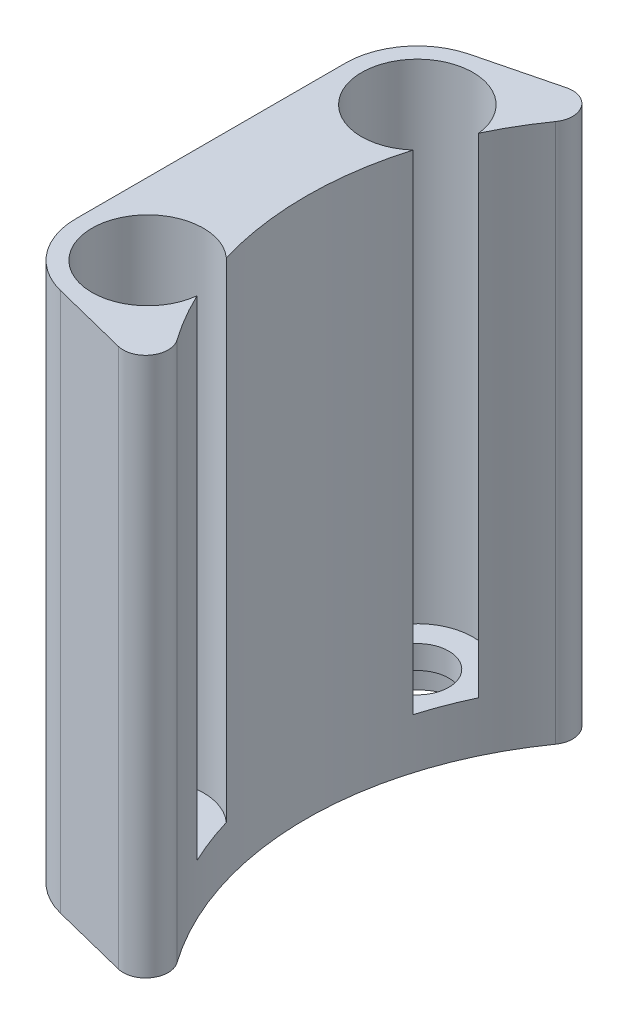
SolidWorks part; units mm, degrees
ref_plane "Plan de face" through (0, 0, 0) normal (0, 0, 1) x (1, 0, 0)
ref_plane "Plan de dessus" through (0, 0, 0) normal (0, 1, 0) x (1, 0, 0)
ref_plane "Plan de droite" through (0, 0, 0) normal (1, 0, 0) x (0, 0, -1)
sketch "Esquisse1" plane through (0, 0, 0) normal (0, 1, 0) x (1, 0, 0)
  line L0 (-31.8551, 22.5) -> (-31.8551, -22.5) construction
  line L1 (-31.8551, 0) -> (0, 0) construction
  circle A0 centre (0, 0) radius 36.5 construction
  arc A1 (-31.8551, 22.5) -> (-31.8551, -22.5) centre (0, 0) ccw construction
  arc A6 (-33.8971, 23.9423) -> (-33.8971, -23.9423) centre (0, 0) ccw
  arc A7 (-29.8131, 21.0577) -> (-29.8131, -21.0577) centre (0, 0) ccw
  arc A8 (-29.8131, 21.0577) -> (-33.8971, 23.9423) centre (-31.8551, 22.5) ccw
  arc A9 (-33.8971, -23.9423) -> (-29.8131, -21.0577) centre (-31.8551, -22.5) ccw
  point P5 (-39, 0)
  point P14 (-31.8551, 0)
  dimension "D1" = 73
  dimension "D3" = 2.5
  dimension "D2" = 45
extrude "Boss.-Extru.1" add sketch "Esquisse1" along normal blind 54.4
sketch "Esquisse2" plane through (0, 54.4, 0) normal (0, 1, 0) x (1, 0, 0)
  line L0 (-35.0124, 10.6368) -> (-33.1512, 15.4923) construction
  line L1 (-35.0124, -10.6368) -> (-33.1512, -15.4923) construction
  line L2 (-39.1309, 15) -> (-39.1309, -15) construction
  circle A0 centre (-39.1309, 15) radius 6 construction
  circle A1 centre (-39.1309, -15) radius 6 construction
  arc A4 (-29.8131, 21.0577) -> (-29.8131, -21.0577) centre (0, 0) ccw construction
  circle A5 centre (-39.1309, 15) radius 6.2
  circle A6 centre (-39.1309, -15) radius 6.2
  point P15 (-34.0818, 13.0645)
  point P16 (-34.0818, -13.0645)
  dimension "D1" = 12
  dimension "D2" = 5.2
  dimension "D4" = 12.4
  dimension "D3" = 30
extrude "Enlèv. mat.-Extru.1" cut sketch "Esquisse2" against normal through all
sketch "Esquisse3" plane through (0, 0, 0) normal (0, -1, 0) x (1, 0, 0)
  line L2 (-47.1309, 15) -> (-47.1309, -15)
  line L3 (-47.1309, 0) -> (-39.1309, 0) construction
  line L4 (-39.1309, 15) -> (-39.1309, -15) construction
  line L5 (-41.0812, 22.7586) -> (-32.4646, 24.9246)
  line L6 (-41.0812, -22.7586) -> (-32.4646, -24.9246)
  arc A0 (-29.8131, -21.0577) -> (-29.8131, 21.0577) centre (0, 0) cw construction
  arc A1 (-29.8131, 21.0577) -> (-33.8971, 23.9423) centre (-31.8551, 22.5) ccw construction
  arc A2 (-33.8971, -23.9423) -> (-29.8131, -21.0577) centre (-31.8551, -22.5) ccw construction
  circle A3 centre (-39.1309, 15) radius 6.2 construction
  circle A4 centre (-39.1309, -15) radius 6.2 construction
  arc A5 (-36.1266, -20.4235) -> (-32.9669, -15.6664) centre (-39.1309, -15) ccw construction
  arc A6 (-32.9669, 15.6664) -> (-34.9917, 10.3841) centre (-39.1309, 15) ccw
  arc A7 (-34.9917, -10.3841) -> (-32.9669, -15.6664) centre (-39.1309, -15) ccw
  arc A8 (-29.8131, 21.0577) -> (-32.9669, 15.6664) centre (0, 0) ccw
  arc A9 (-32.9669, -15.6664) -> (-29.8131, -21.0577) centre (0, 0) ccw
  arc A10 (-34.9917, -10.3841) -> (-34.9917, 10.3841) centre (0, 0) cw
  arc A11 (-32.4646, 24.9246) -> (-29.8131, 21.0577) centre (-31.8551, 22.5) cw
  arc A12 (-32.4646, -24.9246) -> (-29.8131, -21.0577) centre (-31.8551, -22.5) ccw
  circle A13 centre (-39.1309, 15) radius 8 construction
  circle A14 centre (-39.1309, -15) radius 8 construction
  arc A15 (-47.1309, -15) -> (-41.0812, -22.7586) centre (-39.1309, -15) ccw
  arc A16 (-41.0812, 22.7586) -> (-47.1309, 15) centre (-39.1309, 15) ccw
  point P18 (-39.1309, 0)
  dimension "D1" = 8
extrude "Boss.-Extru.2" add sketch "Esquisse3" against normal up to surface (54.4 mm away) up to face at (-38.2914, 54.4, 0)
sketch "Esquisse4" plane through (0, 0, 0) normal (0, -1, 0) x (1, 0, 0)
  line L0 (-47.1309, 15) -> (-47.1309, -15)
  line L1 (-41.0812, 22.7586) -> (-32.4646, 24.9246)
  line L2 (-41.0812, -22.7586) -> (-32.4646, -24.9246)
  arc A0 (-29.8131, 21.0577) -> (-29.8131, -21.0577) centre (0, 0) ccw
  arc A1 (-34.9917, 10.3841) -> (-34.9917, -10.3841) centre (0, 0) ccw construction
  arc A2 (-32.4646, 24.9246) -> (-29.8131, 21.0577) centre (-31.8551, 22.5) cw
  arc A3 (-41.0812, 22.7586) -> (-47.1309, 15) centre (-39.1309, 15) ccw
  arc A4 (-47.1309, -15) -> (-41.0812, -22.7586) centre (-39.1309, -15) ccw
  arc A5 (-32.4646, -24.9246) -> (-29.8131, -21.0577) centre (-31.8551, -22.5) ccw
  arc A6 (-41.0812, 22.7586) -> (-47.1309, 15) centre (-39.1309, 15) ccw construction
  circle A7 centre (-39.1309, 15) radius 3.5
  circle A8 centre (-39.1309, -15) radius 3.5
  dimension "D1" = 7
  dimension "D2" = 7
extrude "Boss.-Extru.3" add sketch "Esquisse4" along normal blind 2.6
sketch "Esquisse5" plane through (0, -2.6, 0) normal (0, -1, 0) x (1, 0, 0)
  line L3 (-32.4646, 24.9246) -> (-41.0812, 22.7586)
  line L4 (-47.1309, 15) -> (-47.1309, -15)
  line L5 (-41.0812, -22.7586) -> (-32.4646, -24.9246)
  line L6 (-32.4646, 24.9246) -> (-41.0812, 22.7586)
  line L7 (-47.1309, 15) -> (-47.1309, -15)
  line L8 (-41.0812, -22.7586) -> (-32.4646, -24.9246)
  circle A0 centre (-39.1309, 15) radius 5.1
  circle A1 centre (-39.1309, -15) radius 5.1
  arc A5 (-29.8131, 21.0577) -> (-32.4646, 24.9246) centre (-31.8551, 22.5) ccw
  arc A6 (-41.0812, 22.7586) -> (-47.1309, 15) centre (-39.1309, 15) ccw
  arc A7 (-47.1309, -15) -> (-41.0812, -22.7586) centre (-39.1309, -15) ccw
  arc A8 (-32.4646, -24.9246) -> (-29.8131, -21.0577) centre (-31.8551, -22.5) ccw
  arc A9 (-29.8131, 21.0577) -> (-29.8131, -21.0577) centre (0, 0) ccw
  arc A10 (-29.8131, 21.0577) -> (-32.4646, 24.9246) centre (-31.8551, 22.5) ccw
  arc A11 (-41.0812, 22.7586) -> (-47.1309, 15) centre (-39.1309, 15) ccw
  arc A12 (-47.1309, -15) -> (-41.0812, -22.7586) centre (-39.1309, -15) ccw
  arc A13 (-32.4646, -24.9246) -> (-29.8131, -21.0577) centre (-31.8551, -22.5) ccw
  arc A14 (-29.8131, 21.0577) -> (-29.8131, -21.0577) centre (0, 0) ccw
  dimension "D2" = 10.2
  dimension "D1" = 0
extrude "Boss.-Extru.4" add sketch "Esquisse5" along normal blind 3
